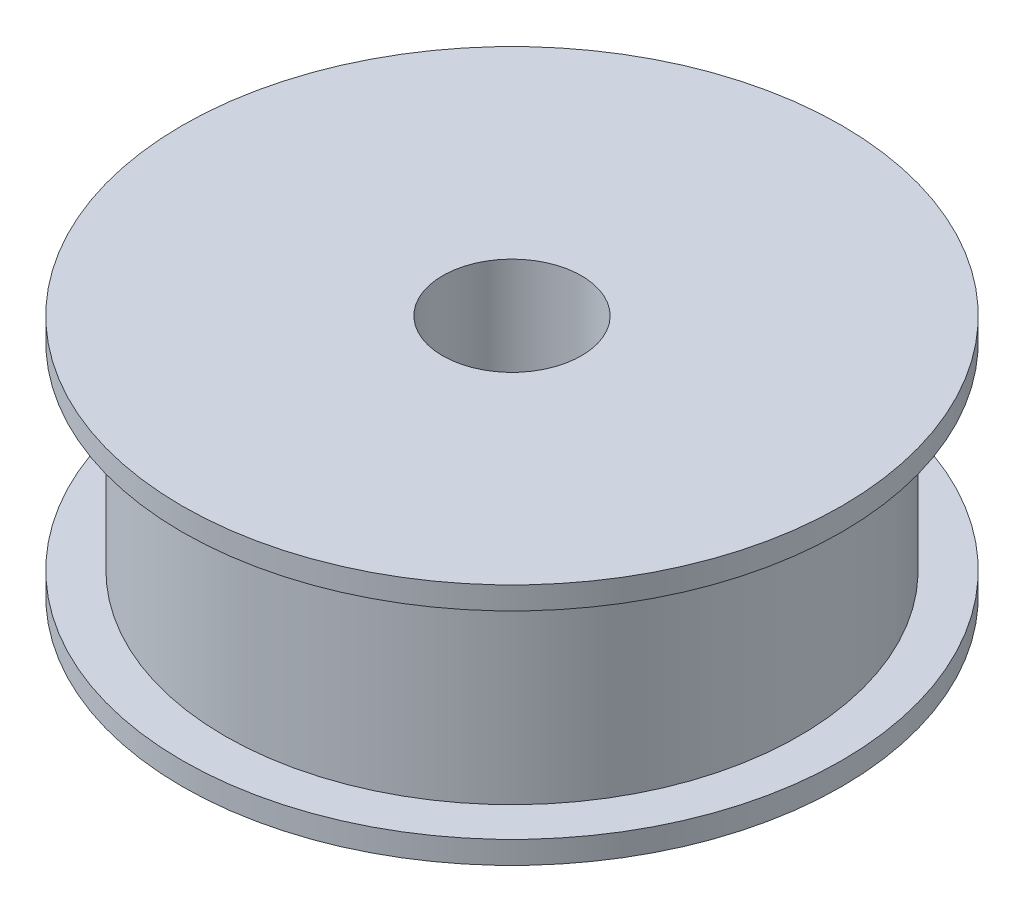
SolidWorks part; units mm, degrees
ref_plane "Front Plane" through (0, 0, 0) normal (0, 0, 1) x (1, 0, 0)
ref_plane "Top Plane" through (0, 0, 0) normal (0, 1, 0) x (1, 0, 0)
ref_plane "Right Plane" through (0, 0, 0) normal (1, 0, 0) x (0, 0, -1)
sketch "Sketch1" plane through (0, 0, 0) normal (1, 0, 0) x (0, 0, -1)
  line L0 (-23.8367, 0) -> (33.8844, 0) construction
  line L1 (-4, -7) -> (-4, 7)
  line L2 (-4, 7) -> (-19, 7)
  line L3 (-19, 7) -> (-19, 5.7)
  line L4 (-19, 5.7) -> (-16.55, 5.7)
  line L5 (-16.55, 5.7) -> (-16.55, -5.7)
  line L7 (-19, -5.7) -> (-16.55, -5.7)
  line L8 (-19, -7) -> (-19, -5.7)
  line L9 (-4, -7) -> (-19, -7)
  point P10 (-16.55, 0)
  point P11 (-4, 0)
  dimension "D1" = 14
  dimension "D2" = 1.3
  dimension "D3" = 16.55
  dimension "D4" = 4
  dimension "D5" = 19
ref_axis "Axis1" through (0, 7.7, 0) along (0, -1, 0)
revolve "Revolve1" add sketch "Sketch1" angle 360 about axis through (0, 7.7, 0) along (0, -1, 0)
